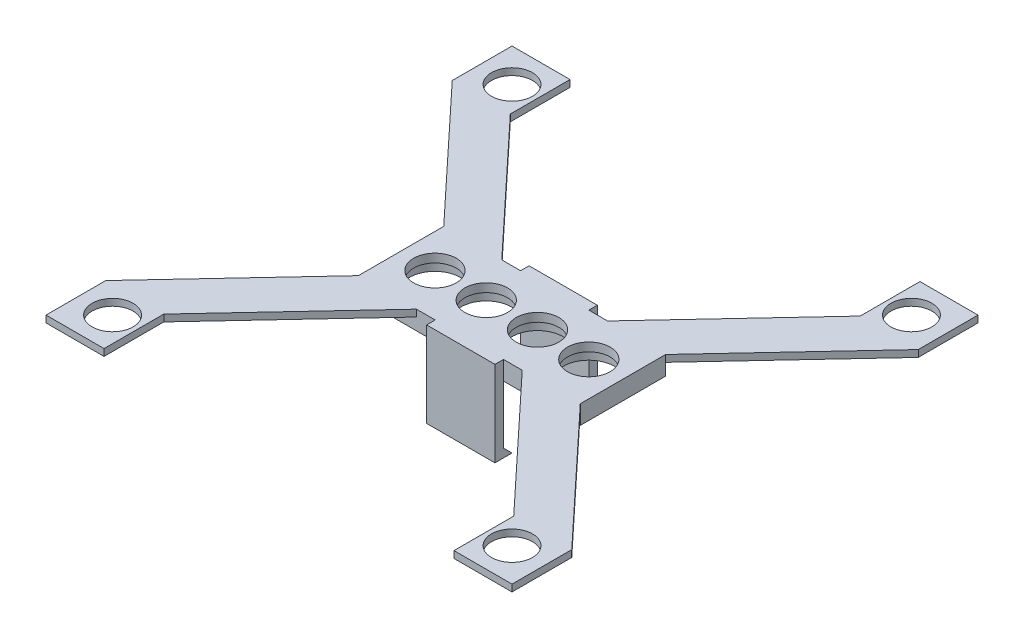
SolidWorks part; units mm, degrees
ref_plane "Přední rovina" through (0, 0, 0) normal (0, 0, 1) x (1, 0, 0)
ref_plane "Horní rovina" through (0, 0, 0) normal (0, 1, 0) x (1, 0, 0)
ref_plane "Pravá rovina" through (0, 0, 0) normal (1, 0, 0) x (0, 0, -1)
sketch "Skica1" plane through (0, 0, 0) normal (0, 0, 1) x (1, 0, 0)
  line L0 (-52.1567, -7.7147) -> (-26.1567, -7.7147)
  line L12 (-52.1567, -6.7147) -> (-26.1567, -6.7147)
  line L15 (-52.1567, -6.7147) -> (-52.1567, -7.7147)
  line L18 (-26.1567, -6.7147) -> (-26.1567, -7.7147)
  point P2 (-39.1567, -7.7147)
  dimension "D1" = 13
  dimension "D2" = 1
extrude "Přidat vysunutím1" add sketch "Skica1" along normal blind 10 contours L0 L18 L12 L15
sketch "Skica2" plane through (0, -7.7147, 0) normal (0, -1, 0) x (-1, 0, 0)
  line L0 (26.1567, -10) -> (26.1567, 0) construction
  line L1 (52.1567, -10) -> (26.1567, -10) construction
  circle A0 centre (48.1867, -5) radius 2.5
  circle A1 centre (42.1767, -5) radius 2.5
  circle A2 centre (36.1667, -5) radius 2.5
  circle A3 centre (30.1567, -5) radius 2.5
  dimension "D1" = 5
  dimension "D3" = 5
  dimension "D5" = 4
  dimension "D4" = 4
extrude "Odebrat vysunutím1" cut sketch "Skica2" against normal blind 1
sketch "Skica3" plane through (0, -6.7147, 0) normal (0, 1, 0) x (1, 0, 0)
  line L0 (-32.9567, 0) -> (-18.6567, 15.3)
  line L25 (-52.1567, 0) -> (-26.1567, 0) construction
  line L27 (-26.1567, 0) -> (-11.8567, 15.3)
  line L29 (-26.1567, 0) -> (-32.9567, 0)
  line L34 (-52.1567, 0) -> (-45.3567, 0)
  line L35 (-52.1567, 0) -> (-66.4567, 15.3)
  line L37 (-45.3567, 0) -> (-59.6567, 15.3)
  line L47 (-45.3567, -10) -> (-59.6567, -25.3)
  line L49 (-52.1567, -10) -> (-66.4567, -25.3)
  line L50 (-52.1567, -10) -> (-45.3567, -10)
  line L51 (-26.1567, -10) -> (-32.9567, -10)
  line L53 (-26.1567, -10) -> (-11.8567, -25.3)
  line L54 (-32.9567, -10) -> (-18.6567, -25.3)
  line L55 (-52.1567, -10) -> (-26.1567, -10) construction
  line L56 (-66.4567, 15.3) -> (-66.4567, 22.3)
  line L57 (-66.4567, 22.3) -> (-59.6567, 22.3)
  line L59 (-59.6567, 22.3) -> (-59.6567, 15.3)
  line L60 (-59.6567, -25.3) -> (-59.6567, -32.3)
  line L61 (-59.6567, -32.3) -> (-66.4567, -32.3)
  line L62 (-66.4567, -32.3) -> (-66.4567, -25.3)
  line L63 (-18.6567, -25.3) -> (-18.6567, -32.3)
  line L64 (-18.6567, -32.3) -> (-11.8567, -32.3)
  line L65 (-11.8567, -32.3) -> (-11.8567, -25.3)
  line L66 (-11.8567, 15.3) -> (-11.8567, 22.3)
  line L67 (-11.8567, 22.3) -> (-18.6567, 22.3)
  line L68 (-18.6567, 22.3) -> (-18.6567, 15.3)
  circle A0 centre (-62.5567, 18.4) radius 2.4
  circle A1 centre (-15.7567, 18.4) radius 2.4
  circle A2 centre (-62.5567, -28.4) radius 2.4
  circle A3 centre (-15.7567, -28.4) radius 2.4
  point P18 (0, 0)
  dimension "D7" = 6.8
  dimension "D9" = 4.8
  dimension "D14" = 4.8
  dimension "D18" = 4.8
  dimension "D31" = 4.8
  dimension "D3" = 7
  dimension "D10" = 6.8
  dimension "D11" = 0
  dimension "D12" = 3.9
  dimension "D13" = 3.9
  dimension "D15" = 7
  dimension "D16" = 0
  dimension "D17" = 3.9
  dimension "D19" = 3.9
  dimension "D20" = 3.9
  dimension "D21" = 6.8
  dimension "D22" = 6.8
  dimension "D23" = 6.8
  dimension "D24" = 0
  dimension "D25" = 6.8
  dimension "D26" = 54.6
  dimension "D27" = 54.6
  dimension "D28" = 6.8
  dimension "D29" = 54.6
  dimension "D30" = 54.6
  dimension "D32" = 3.9
  dimension "D33" = 6.8
  dimension "D34" = 3.9
  dimension "D35" = 3.9
  dimension "D36" = 22.3
  dimension "D37" = 22.3
  dimension "D38" = 10
  dimension "D39" = 10
extrude "Přidat vysunutím2" add sketch "Skica3" against normal blind 0.8
sketch "Skica4" plane through (0, -7.7147, 0) normal (0, -1, 0) x (-1, 0, 0)
  line L1 (52.1567, -10) -> (26.1567, -10)
  line L2 (52.1567, -10) -> (52.1567, 0)
  line L3 (52.1567, 0) -> (26.1567, 0)
  line L4 (26.1567, -10) -> (26.1567, 0)
  circle A0 centre (48.1867, -5) radius 3
  circle A1 centre (42.1767, -5) radius 3
  circle A2 centre (36.1667, -5) radius 3
  circle A3 centre (30.1567, -5) radius 3
  point P18 (0, 0)
  point P19 (0, 0)
  point P20 (0, 0)
  dimension "D1" = 6
  dimension "D2" = 6
  dimension "D3" = 6
  dimension "D4" = 6
extrude "Přidat vysunutím3" add sketch "Skica4" along normal blind 1.2
sketch "Skica6" plane through (0, -6.7147, 0) normal (0, 1, 0) x (1, 0, 0)
  line L0 (-45.3567, 0) -> (-32.9567, 0) construction
  line L1 (-43.1567, 0) -> (-35.1567, 0)
  line L2 (-43.1567, 0) -> (-43.1567, 1)
  line L3 (-43.1567, 1) -> (-35.1567, 1)
  line L4 (-35.1567, 0) -> (-35.1567, 1)
  line L5 (-45.3567, -10) -> (-32.9567, -10) construction
  line L6 (-43.1567, -10) -> (-35.1567, -10)
  line L7 (-43.1567, -10) -> (-43.1567, -11)
  line L8 (-43.1567, -11) -> (-35.1567, -11)
  line L9 (-35.1567, -10) -> (-35.1567, -11)
  dimension "D1" = 1
  dimension "D2" = 8
  dimension "D3" = 2.2
  dimension "D4" = 2.2
  dimension "D5" = 1
extrude "Přidat vysunutím5" add sketch "Skica6" against normal blind 10
sketch "Skica7" plane through (-35.1567, 0, 0) normal (1, 0, 0) x (0, 0, -1)
  line L0 (0, -16.7147) -> (-1, -16.7147)
  line L1 (-1, -16.7147) -> (0, -15.7147)
  line L2 (0, -16.7147) -> (0, -8.9147) construction
  line L3 (0, -15.7147) -> (0, -16.7147)
  line L4 (-10, -16.7147) -> (-9, -16.7147)
  line L5 (-9, -16.7147) -> (-10, -15.7147)
  line L6 (-10, -16.7147) -> (-10, -8.9147) construction
  line L7 (-10, -15.7147) -> (-10, -16.7147)
  dimension "D1" = 1
  dimension "D2" = 1
extrude "Přidat vysunutím6" add sketch "Skica7" against normal blind 8
